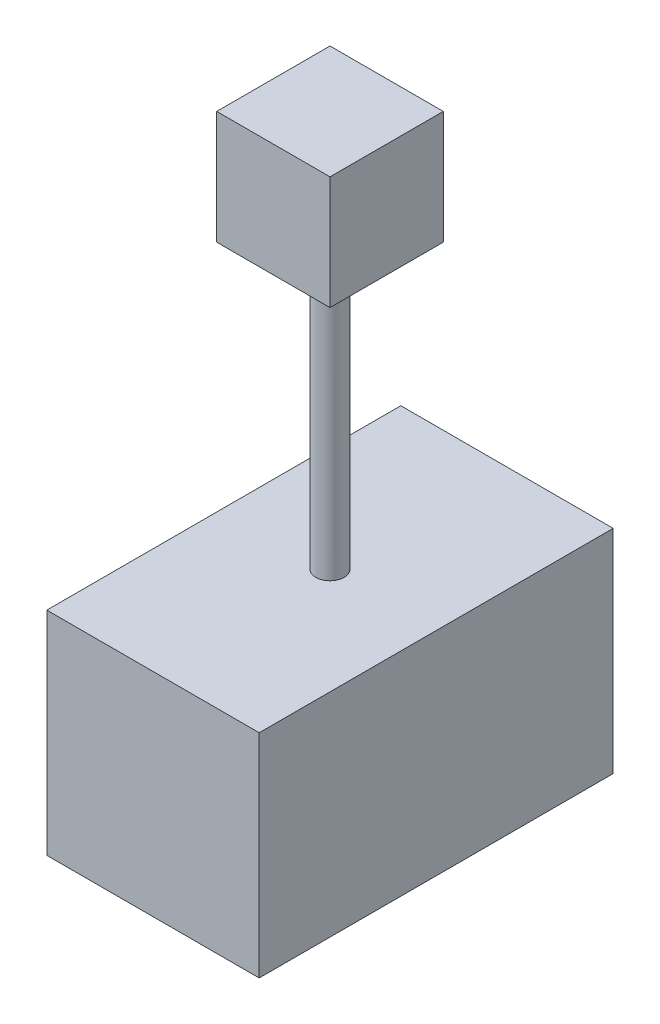
SolidWorks part; units mm, degrees
ref_plane "Face" through (0, 0, 0) normal (0, 0, 1) x (1, 0, 0)
ref_plane "Dessus" through (0, 0, 0) normal (0, 1, 0) x (1, 0, 0)
ref_plane "Droite" through (0, 0, 0) normal (1, 0, 0) x (0, 0, -1)
sketch "Esquisse1" plane through (0, 0, 0) normal (0, 1, 0) x (1, 0, 0)
  line L1 (0, 0) -> (150, 0)
  line L2 (0, 0) -> (0, 250)
  line L3 (0, 250) -> (150, 250)
  line L4 (150, 0) -> (150, 250)
  dimension "D1" = 150
  dimension "D2" = 250
extrude "Extrusion1" add sketch "Esquisse1" along normal blind 150
sketch "Esquisse2" plane through (0, 150, 0) normal (0, 1, 0) x (1, 0, 0)
  line L0 (75, 250) -> (75, 0) construction
  line L1 (150, 250) -> (0, 250) construction
  line L2 (0, 0) -> (150, 0) construction
  circle A0 centre (75, 125) radius 10
  dimension "D1" = 20
extrude "Extrusion2" add sketch "Esquisse2" along normal blind 200
sketch "Esquisse3" plane through (0, 350, 0) normal (0, 1, 0) x (1, 0, 0)
  line L1 (35, 165) -> (115, 165)
  line L2 (35, 165) -> (35, 85)
  line L3 (35, 85) -> (115, 85)
  line L4 (115, 165) -> (115, 85)
  circle A0 centre (75, 125) radius 10 construction
  dimension "D1" = 80
  dimension "D2" = 80
  dimension "D3" = 40
  dimension "D4" = 40
extrude "Extrusion3" add sketch "Esquisse3" along normal blind 80
